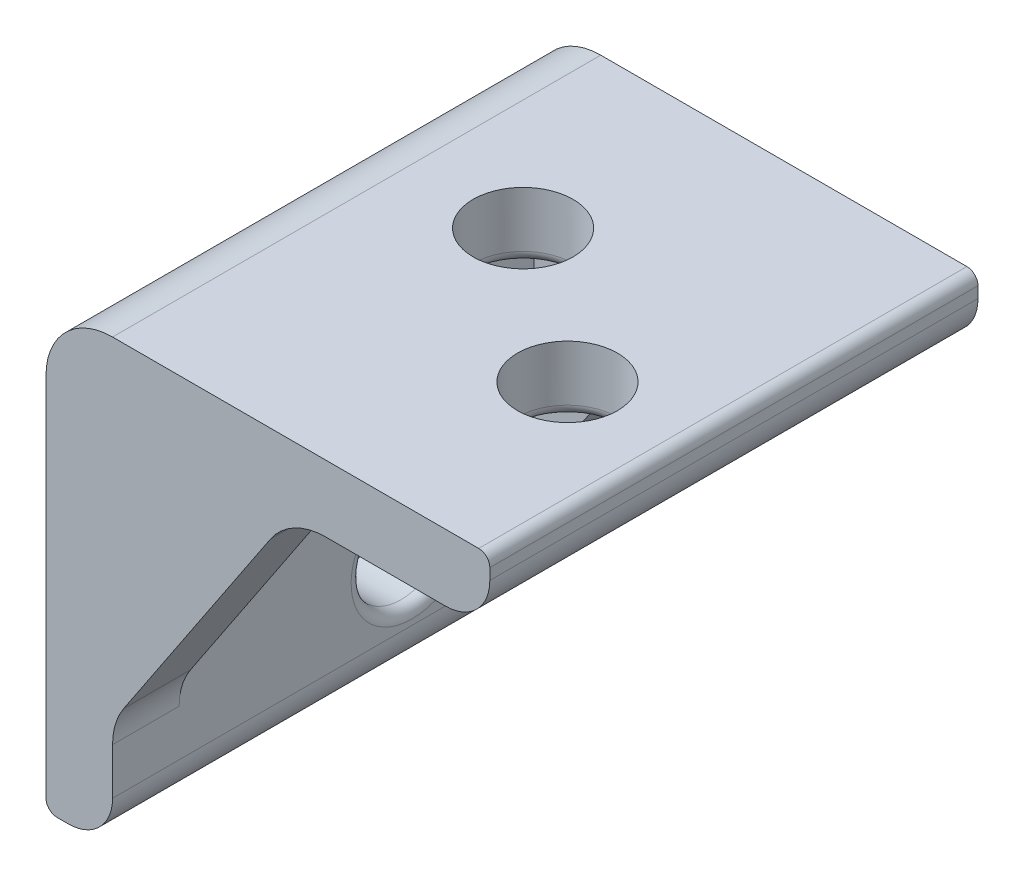
SolidWorks part; units mm, degrees
material "自定义塑料"
ref_plane "前视基准面" through (0, 0, 0) normal (0, 0, 1) x (1, 0, 0)
ref_plane "上视基准面" through (0, 0, 0) normal (0, 1, 0) x (1, 0, 0)
ref_plane "右视基准面" through (0, 0, 0) normal (1, 0, 0) x (0, 0, -1)
sketch "草图1" plane through (0, 0, 0) normal (0, 0, 1) x (1, 0, 0)
  line L1 (-17, 0) -> (-17, -15)
  line L2 (-19, -17) -> (-19.5, -17)
  line L3 (-20, -16.5) -> (-20, 3)
  line L5 (0, -55) -> (0, 55) construction
  line L9 (-20, 3) -> (-0.5, 3)
  line L10 (-17, 0) -> (-2, 0)
  line L14 (0, 2.5) -> (0, 2)
  arc A0 (-20, -16.5) -> (-19.5, -17) centre (-19.5, -16.5) ccw
  arc A1 (-17, -15) -> (-19, -17) centre (-19, -15) cw
  arc A2 (0, 2) -> (-2, 0) centre (-2, 2) cw
  arc A3 (0, 2.5) -> (-0.5, 3) centre (-0.5, 2.5) ccw
  point P11 (0, 0)
  point P15 (0, 0)
  point P17 (-20, -17)
  point P20 (-17, -17)
  point P21 (0, 3)
  point P23 (0, 0)
  point P24 (0, 3)
  dimension "D5" = 0.5
  dimension "D6" = 2
  dimension "D7" = 2
  dimension "D8" = 0.5
  dimension "D1" = 20
  dimension "D2" = 3
  dimension "D3" = 3
  dimension "D4" = 20
extrude "凸台-拉伸1" add sketch "草图1" along normal mid plane 22
sketch "草图2" plane through (-17, 0, 0) normal (1, 0, 0) x (0, 0, -1)
  line L1 (2.5, -12) -> (-2.5, -5) construction
  line L5 (-11, -17) -> (11, -17) construction
  circle A0 centre (2.5, -12) radius 2.25
  circle A1 centre (-2.5, -5) radius 2.25
  point P4 (0, -8.5)
  dimension "D1" = 4.5
  dimension "D4" = 4.5
  dimension "D2" = 5
  dimension "D5" = 7
  dimension "D6" = 5
sketch "草图4" plane through (0, 0, 0) normal (0, 1, 0) x (1, 0, 0)
  line L1 (0, -11) -> (0, 11) construction
  line L2 (-12, 2.5) -> (-5, -2.5) construction
  circle A0 centre (-5, -2.5) radius 2.25
  circle A1 centre (-12, 2.5) radius 2.25
  point P2 (-8.5, 0)
  dimension "D4" = 7
  dimension "D6" = 4.5
  dimension "D3" = 5
  dimension "D5" = 5
extrude "切除-拉伸1" cut sketch "草图4" along normal blind 10
extrude "切除-拉伸2" cut sketch "草图2" against normal blind 20
fillet "圆角2" radius 0.5 4 edges at (-17, -12, -4.75) (-5, 0, 4.75) (-17, -5, 0.25) (-12, 0, -0.25)
sketch "草图5" plane through (0, 0, -11) normal (0, 0, 1) x (1, 0, 0)
  line L0 (-9, 0) -> (-17, -12)
  line L1 (-17, 0) -> (-2, 0) construction
  line L2 (-17, -15) -> (-17, 0) construction
  dimension "D1" = 12
  dimension "D2" = 8
rib "筋2" sketch "草图5" sketch "草图5" thickness 3 parameters "D1"=3
sketch "草图6" plane through (0, 0, 11) normal (0, 0, -1) x (-1, 0, 0)
  line L0 (9, 0) -> (17, -12)
rib "筋3" sketch "草图6" sketch "草图6" thickness 3 parameters "D1"=3
fillet "圆角3" radius 3 5 edges at (-20, 3, 0) (-17, -12, 9.5) (-9, 0, 9.5) (-9, 0, -9.5) (-17, -12, -9.5)
